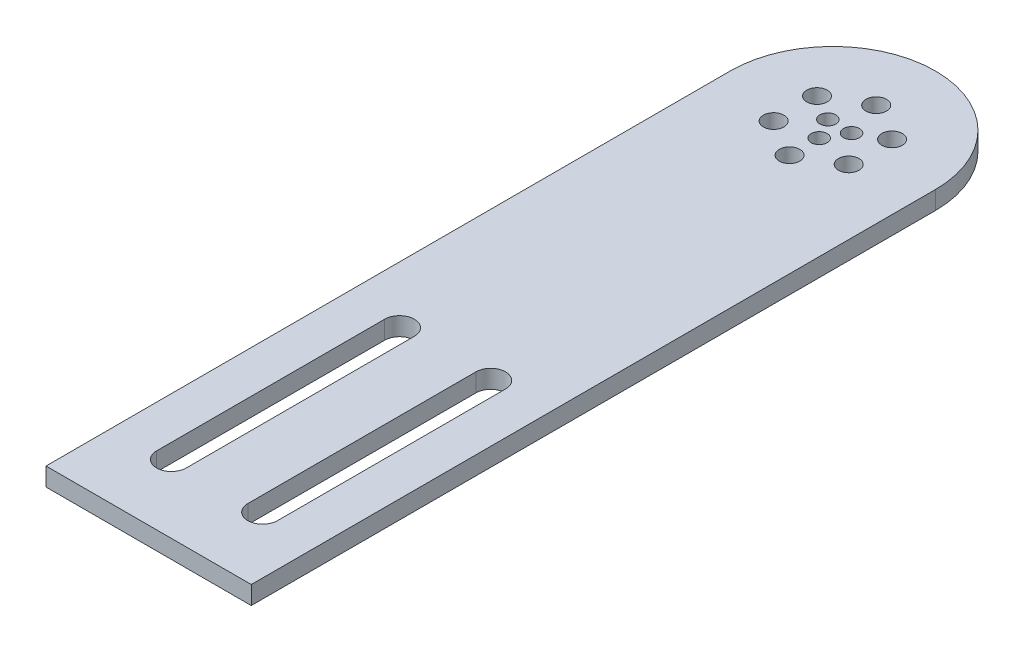
SolidWorks part; units mm, degrees
ref_plane "Front Plane" through (0, 0, 0) normal (0, 0, 1) x (1, 0, 0)
ref_plane "Top Plane" through (0, 0, 0) normal (0, 1, 0) x (1, 0, 0)
ref_plane "Right Plane" through (0, 0, 0) normal (1, 0, 0) x (0, 0, -1)
sketch "Sketch1" plane through (0, 0, 0) normal (0, 1, 0) x (1, 0, 0)
  line L1 (-22.5, 75) -> (22.5, 75)
  line L2 (-22.5, 75) -> (-22.5, -75)
  line L3 (-22.5, -75) -> (22.5, -75)
  line L4 (22.5, 75) -> (22.5, -75)
  line L5 (0, -75) -> (0, 75) construction
  line L6 (-22.5, 0) -> (22.5, 0) construction
  point P0 (0, 0)
  dimension "D1" = 150
  dimension "D2" = 45
extrude "Boss-Extrude1" add sketch "Sketch1" along normal blind 4
sketch "Sketch2" plane through (0, 0, 0) normal (0, 1, 0) x (1, 0, 0)
  line L0 (22.5, 75) -> (-22.5, 75) construction
  circle A0 centre (0, 75) radius 22.5
extrude "Boss-Extrude2" add sketch "Sketch2" along normal blind 4
sketch "Sketch3" plane through (0, 4, 0) normal (0, 1, 0) x (1, 0, 0)
  line L0 (0, 75) -> (0, 84.5) construction
  circle A0 centre (0, 84.5) radius 2.25
  dimension "D1" = 4.5
  dimension "D2" = 9.5
extrude "Cut-Extrude1" cut sketch "Sketch3" against normal through all
pattern_circular "CirPattern1" count 6 over 360 about axis through (0, 0, -75) along (0, 1, 0) of "Cut-Extrude1"
sketch "Sketch4" plane through (0, 4, 0) normal (0, 1, 0) x (1, 0, 0)
  line L0 (0, 75) -> (0, 72) construction
  circle A0 centre (0, 72) radius 1.75
  dimension "D1" = 3.5
  dimension "D2" = 3
extrude "Cut-Extrude2" cut sketch "Sketch4" against normal blind 4
pattern_circular "CirPattern2" count 3 over 360 about axis through (0, 0, -75) along (0, 1, 0) of "Cut-Extrude2"
sketch "Sketch5" plane through (0, 4, 0) normal (0, 1, 0) x (1, 0, 0)
  line L0 (0, -75) -> (0, -35) construction
  line L1 (-22.5, -75) -> (22.5, -75) construction
  line L2 (0, -35) -> (-10, -35) construction
  line L3 (-10, -10) -> (-10, -60) construction
  line L4 (-6.75, -10) -> (-6.75, -60)
  line L5 (-13.25, -10) -> (-13.25, -60)
  line L6 (-22.5, 75) -> (-22.5, -75) construction
  arc A0 (-6.75, -10) -> (-13.25, -10) centre (-10, -10) ccw
  arc A1 (-13.25, -60) -> (-6.75, -60) centre (-10, -60) ccw
  point P8 (-10, -35)
  dimension "D1" = 6.5
  dimension "D2" = 12.5
  dimension "D3" = 50
  dimension "D4" = 40
extrude "Cut-Extrude3" cut sketch "Sketch5" against normal blind 4
mirror "Mirror1" about plane through (0, 0, 0) normal (1, 0, 0) of "Cut-Extrude3"
